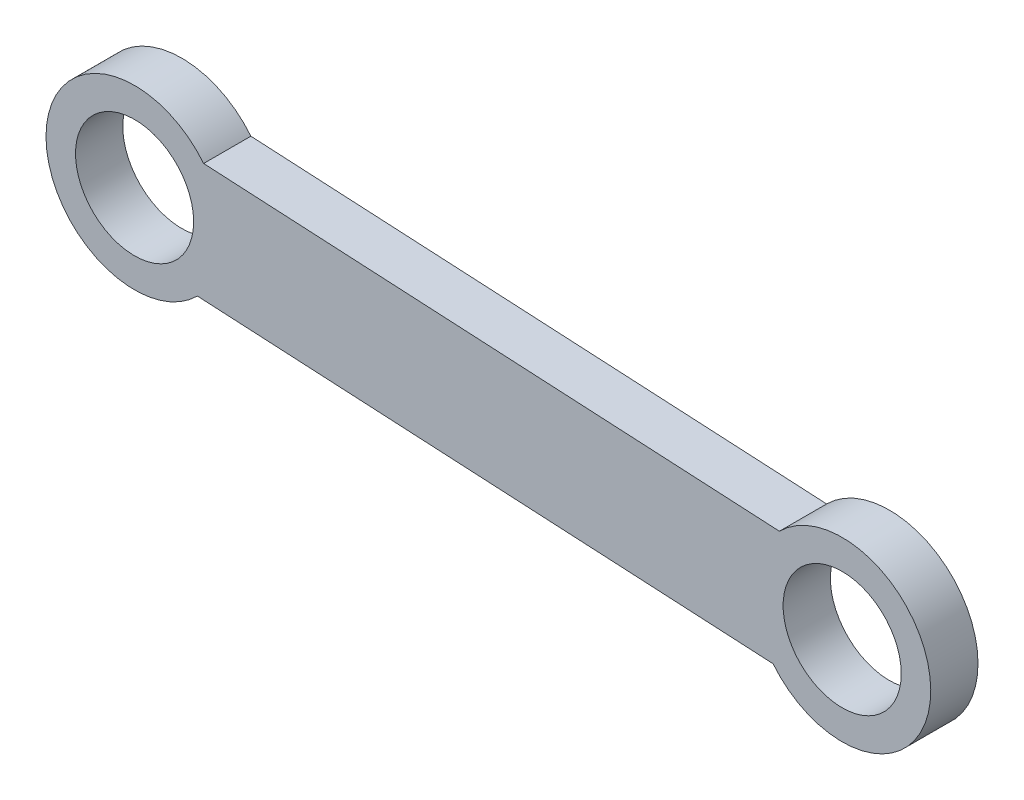
SolidWorks part; units mm, degrees
ref_plane "Front Plane" through (0, 0, 0) normal (0, 0, 1) x (1, 0, 0)
ref_plane "Top Plane" through (0, 0, 0) normal (0, 1, 0) x (1, 0, 0)
ref_plane "Right Plane" through (0, 0, 0) normal (1, 0, 0) x (0, 0, -1)
sketch "Sketch1" plane through (0, 0, 0) normal (0, 0, 1) x (0.4312, 0.9023, 0)
  line L0 (-23.2742, 28.2643) -> (-18.6548, 30.1777) construction
  line L1 (-18.6548, 30.1777) -> (-27.8936, 26.3509) construction
  line L2 (-18.6548, 30.1777) -> (-41.6158, 85.6105)
  line L3 (-27.8936, 26.3509) -> (-50.8546, 81.7837)
  line L4 (-41.6158, 85.6105) -> (-50.8546, 81.7837) construction
  arc A1 (-27.8936, 26.3509) -> (-18.6548, 30.1777) centre (-23.2742, 28.2643) ccw
  arc A2 (-50.8546, 81.7837) -> (-41.6158, 85.6105) centre (-46.2352, 83.6971) cw
  circle A4 centre (-46.2352, 83.6971) radius 5
  circle A5 centre (-46.2352, 83.6971) radius 7.5
  circle A6 centre (-23.2742, 28.2643) radius 5
  circle A7 centre (-23.2742, 28.2643) radius 7.5
  dimension "D1" = 10
  dimension "D3" = 5
  dimension "D6" = 5
  dimension "D2" = 60
extrude "Boss-Extrude1" add sketch "Sketch1" along normal blind 4 contours A7 L2 A5 L3 | L3 A5 L2 A4 | L2 A5 L3 A2 | L3 A7 L2 A1 | L2 A7 L3 A6
move or copy body "Body-Move/Copy1" [suppressed] bodies to move or copy 101
